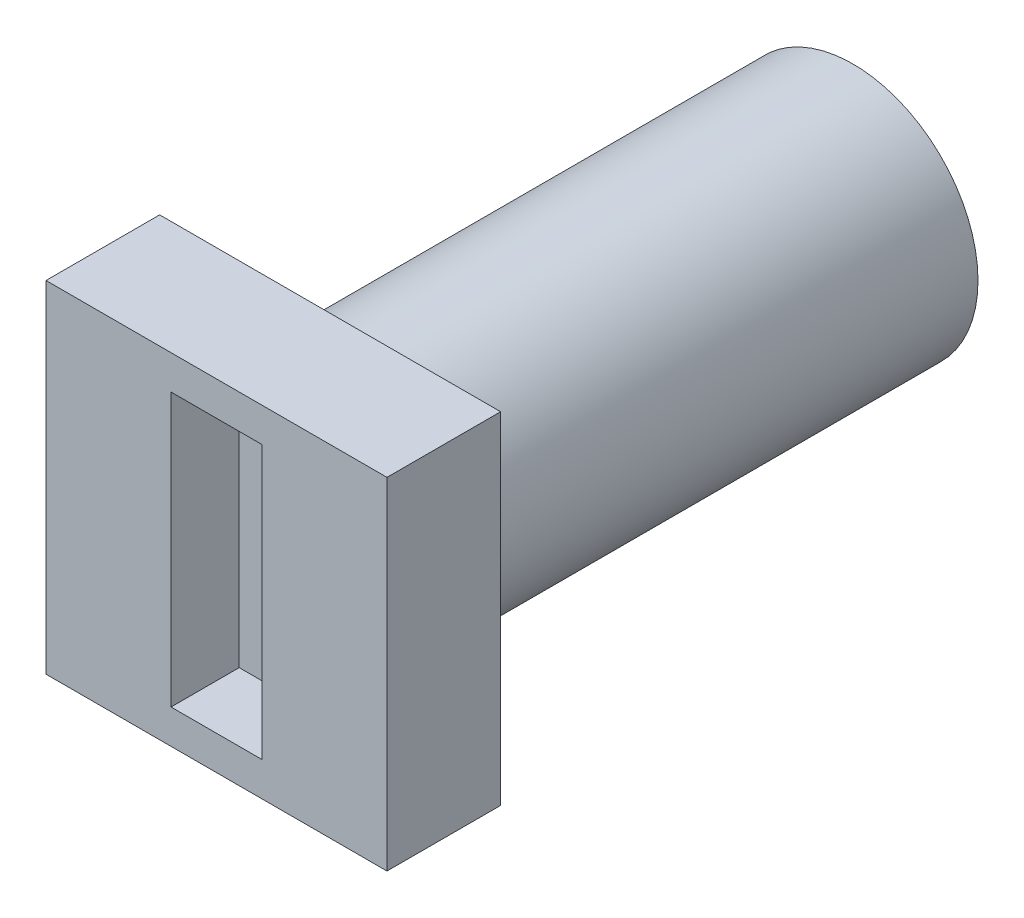
SolidWorks part; units mm, degrees
ref_plane "Plan de face" through (0, 0, 0) normal (0, 0, 1) x (1, 0, 0)
ref_plane "Plan de dessus" through (0, 0, 0) normal (0, 1, 0) x (1, 0, 0)
ref_plane "Plan de droite" through (0, 0, 0) normal (1, 0, 0) x (0, 0, -1)
sketch "Esquisse1" plane through (0, 0, 0) normal (0, 0, 1) x (1, 0, 0)
  line L0 (-2, 1.5) -> (-2, -1.5)
  line L1 (-5, 2.2913) -> (-5, -2.2913)
  arc A0 (-2, 1.5) -> (-2, -1.5) centre (0, 0) cw
  arc A1 (-5, 2.2913) -> (-5, -2.2913) centre (0, 0) cw
  dimension "D2" = 2.5
  dimension "D1" = 2
  dimension "D4" = 4.5826
  dimension "D3" = 3
extrude "Boss.-Extru.1" add sketch "Esquisse1" along normal blind 23
hole_wizard "Diamètre du perçage Ø2.0 (2)1" positions "Esquisse3D1" profile "Esquisse3" hole size "Ø2.0" standard "Ansi Metric" end condition up to next
sketch3d "Esquisse3D1"
  line L6 (-5, -0.0013, 11.5) -> (-5, -0.0013, 3.5) construction
  line L8 (-5, -2.2913, 23) -> (-5, -2.2913, 0) construction
  line L9 (-5, 2.2913, 0) -> (-5, -2.2913, 0) construction
  point P0 (-5, -0.0013, 3.5)
  point P2 (-5, -0.0013, 11.5)
  point P36 (-5, 0, 0)
  point P39 (0, 0, 0)
  point P40 (0, 0, 0)
  dimension "D1" = 8
  dimension "D2" = 3.5
  dimension "D3" = 2.29
sketch "Esquisse3" plane through (-5, -0.0013, 3.5) normal (0, 1, 0) x (0, 0, 1)
  line L0 (0, 0) -> (0, 3)
  line L1 (0, 3) -> (1, 3)
  line L2 (1, 3) -> (1, 0)
  line L5 (1, 0) -> (0, 0)
  line L11 (0, -6.35) -> (0, 107.95) construction
  dimension "Diamètre du perçage jusqu'au prochain" = 2
  dimension "Profondeur du perçage jusqu'au prochain" = 3
sketch "Esquisse4" plane through (0, 0, 23) normal (0, 0, 1) x (1, 0, 0)
  line L1 (-7.5, 7.5) -> (7.5, 7.5)
  line L2 (-7.5, 7.5) -> (-7.5, -7.5)
  line L3 (-7.5, -7.5) -> (7.5, -7.5)
  line L4 (7.5, 7.5) -> (7.5, -7.5)
  arc A4 (-2, -1.5) -> (-2, 1.5) centre (0, 0) ccw construction
  dimension "D3" = 7.5
  dimension "D1" = 15
  dimension "D2" = 15
  dimension "D4" = 7.5
extrude "Boss.-Extru.3" add sketch "Esquisse4" along normal blind 2
sketch "Esquisse6" plane through (0, 0, 25) normal (0, 0, 1) x (1, 0, 0)
  line L1 (-7.5, 7.5) -> (7.5, 7.5)
  line L2 (-7.5, 7.5) -> (-7.5, -7.5)
  line L3 (-7.5, -7.5) -> (7.5, -7.5)
  line L4 (7.5, 7.5) -> (7.5, -7.5)
  line L5 (-2, 6) -> (2, 6)
  line L6 (-2, 6) -> (-2, -6)
  line L7 (-2, -6) -> (2, -6)
  line L8 (2, 6) -> (2, -6)
  dimension "D1" = 4
  dimension "D2" = 5.5
  dimension "D3" = 12
  dimension "D4" = 1.5
extrude "Boss.-Extru.4" add sketch "Esquisse6" along normal blind 3
